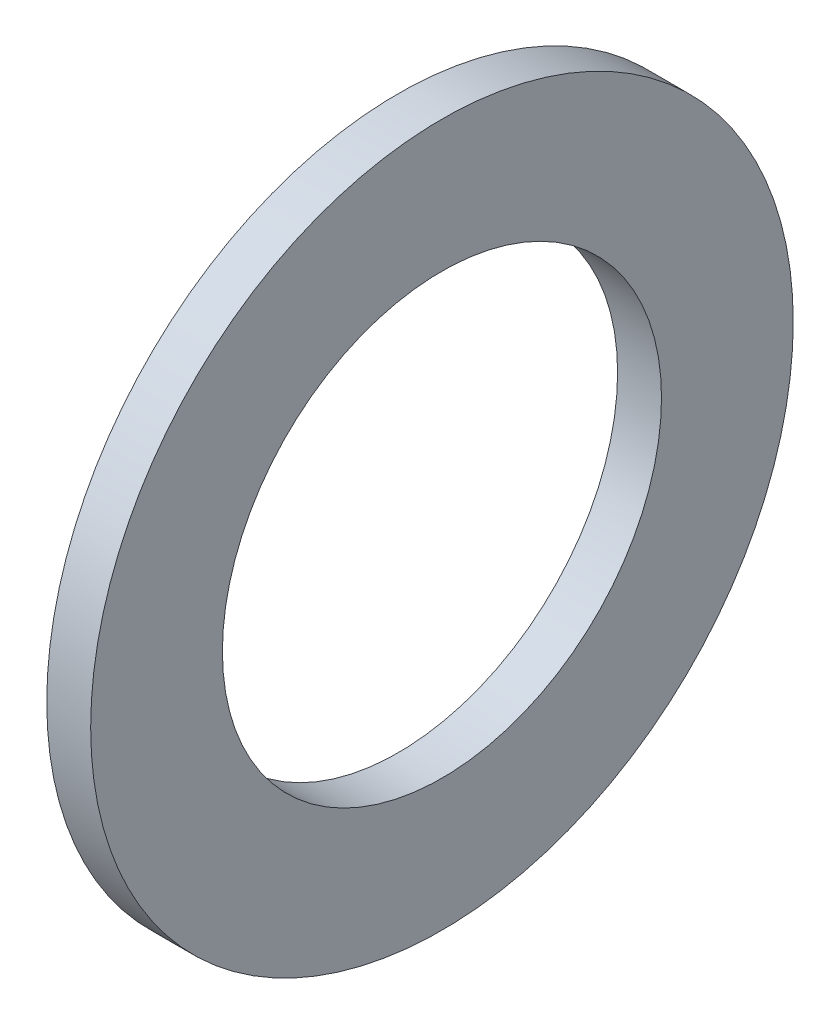
SolidWorks part; units mm, degrees
ref_plane "Front Plane" through (0, 0, 0) normal (0, 0, 1) x (1, 0, 0)
ref_plane "Top Plane" through (0, 0, 0) normal (0, 1, 0) x (1, 0, 0)
ref_plane "Right Plane" through (0, 0, 0) normal (1, 0, 0) x (0, 0, -1)
sketch "Sketch1" plane through (0, 0, 0) normal (1, 0, 0) x (0, 0, -1)
  circle A0 centre (0, 0) radius 25
  circle A1 centre (0, 0) radius 40
  dimension "D1" = 50
  dimension "D2" = 15
extrude "Boss-Extrude1" add sketch "Sketch1" along normal blind 5
